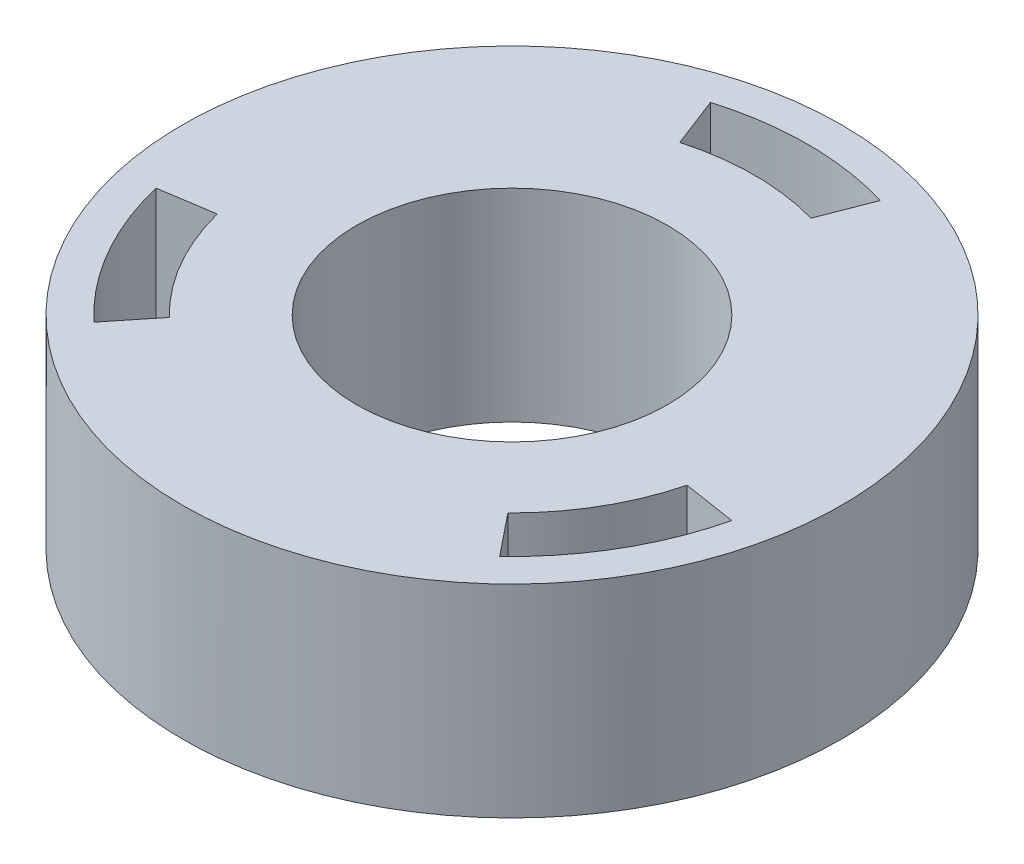
SolidWorks part; units mm, degrees
ref_plane "Front Plane" through (0, 0, 0) normal (0, 0, 1) x (1, 0, 0)
ref_plane "Top Plane" through (0, 0, 0) normal (0, 1, 0) x (1, 0, 0)
ref_plane "Right Plane" through (0, 0, 0) normal (1, 0, 0) x (0, 0, -1)
sketch "Sketch1" plane through (0, 0, 0) normal (0, 1, 0) x (1, 0, 0)
  circle A0 centre (0, 0) radius 19.36
  dimension "D1" = 38.72
extrude "Boss-Extrude1" add sketch "Sketch1" along normal blind 10
sketch "Sketch2" plane through (0, 0, 0) normal (0, -1, 0) x (1, 0, 0)
  line L0 (10.0295, 10.2771) -> (13.1759, 14.1847)
  line L1 (13.915, 3.5473) -> (18.8723, 4.3183)
  line L2 (13.915, 3.5473) -> (17.0517, 4.0351) construction
  line L3 (-3.8855, -13.8244) -> (-5.6964, -18.503)
  line L4 (3.8855, -13.8244) -> (5.6964, -18.503)
  line L5 (-10.0295, 10.2771) -> (-13.1759, 14.1847)
  line L6 (-13.915, 3.5473) -> (-18.8723, 4.3183)
  circle A0 centre (0, 0) radius 14.36
  circle A1 centre (0, 0) radius 19.36 construction
  circle A2 centre (0, 0) radius 19.36
  point P25 (0, 0)
  circle M3 centre (0, 0) radius 19.36
  dimension "D1" = 3
extrude "Cut-Extrude1" cut sketch "Sketch2" against normal up to next contours A0 L1 L0 M3 | A0 L5 L6 M3 | A0 L3 L4 M3
sketch "Sketch3" plane through (0, 0, 0) normal (0, -1, 0) x (1, 0, 0)
  circle A1 centre (0, 0) radius 9.21
extrude "Cut-Extrude2" cut sketch "Sketch3" against normal up to next
sketch "Sketch4" plane through (0, 0, 0) normal (0, -1, 0) x (1, 0, 0)
  circle A0 centre (0, 0) radius 19.36
  circle A1 centre (0, 0) radius 9.21
extrude "Boss-Extrude2" add sketch "Sketch4" along normal blind 2
sketch "Sketch5" plane through (0, -2, 0) normal (0, -1, 0) x (1, 0, 0)
  circle A0 centre (0, 0) radius 19.5226
  circle A1 centre (0, 0) radius 17.5226
  dimension "D1" = 2
extrude "Boss-Extrude3" add sketch "Sketch5" against normal up to surface (12 mm away) up to face at (0, 10, 9.21)
